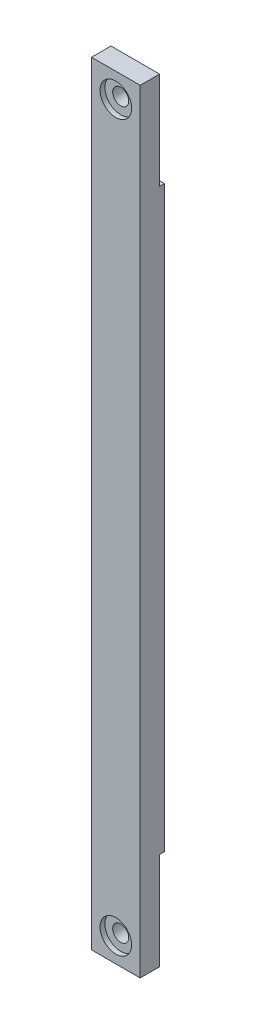
SolidWorks part; units mm, degrees
ref_plane "前视基准面" through (0, 0, 0) normal (0, 0, 1) x (1, 0, 0)
ref_plane "上视基准面" through (0, 0, 0) normal (0, 1, 0) x (1, 0, 0)
ref_plane "右视基准面" through (0, 0, 0) normal (1, 0, 0) x (0, 0, -1)
other "Configuration Table"
sketch "草图1" plane through (0, 0, 0) normal (0, 0, 1) x (1, 0, 0)
  line L1 (0, 0) -> (10, 0)
  line L2 (0, 0) -> (0, -159)
  line L3 (0, -159) -> (10, -159)
  line L4 (10, 0) -> (10, -159)
  line L5 (0, 0) -> (10, -159) construction
  line L6 (0, -159) -> (10, 0) construction
  point P4 (5, -79.5)
  dimension "D1" = 10
  dimension "D2" = 159
extrude "凸台-拉伸1" add sketch "草图1" along normal blind 5
sketch "草图3" plane through (0, 0, 0) normal (0, 0, -1) x (-1, 0, 0)
  line L0 (0, 0) -> (0, -159) construction
  line L1 (-10, 0) -> (0, 0)
  line L2 (-10, 0) -> (-10, -20)
  line L3 (-10, -20) -> (0, -20)
  line L4 (0, 0) -> (0, -20)
  line L5 (-10, 0) -> (0, -20) construction
  line L6 (-10, -20) -> (0, 0) construction
  line L8 (-10, -159) -> (0, -159)
  line L9 (-10, -159) -> (-10, -139)
  line L10 (-10, -139) -> (0, -139)
  line L11 (0, -159) -> (0, -139)
  line L12 (-10, -159) -> (0, -139) construction
  line L13 (-10, -139) -> (0, -159) construction
  point P4 (-5, -10)
  point P12 (-5, -149)
  dimension "D1" = 20
  dimension "D2" = 20
extrude "切除-拉伸1" cut sketch "草图3" against normal blind 1
sketch "草图7" plane through (0, 0, 5) normal (0, 0, 1) x (1, 0, 0)
  line L0 (10, -159) -> (10, 0) construction
  line L1 (0, 0) -> (10, 0) construction
  line L2 (0, 0) -> (0, -10) construction
  line L3 (0, -10) -> (10, -10) construction
  line L4 (10, 0) -> (10, -10) construction
  line L5 (0, 0) -> (10, -10) construction
  line L6 (0, -10) -> (10, 0) construction
  line L8 (0, -159) -> (10, -159) construction
  line L9 (0, -159) -> (0, -149) construction
  line L10 (0, -149) -> (10, -149) construction
  line L11 (10, -159) -> (10, -149) construction
  line L12 (0, -159) -> (10, -149) construction
  line L13 (0, -149) -> (10, -159) construction
  circle A0 centre (5, -5) radius 3.25
  circle A1 centre (5, -154) radius 3.25
  point P4 (5, -5)
  point P12 (5, -154)
  dimension "D3" = 6.5
  dimension "D4" = 6.5
  dimension "D1" = 10
  dimension "D2" = 10
hole_wizard "M4 螺纹孔的螺纹孔钻头1" positions "草图8" profile "草图9" hole size "M4" standard "ISO" end condition through all
sketch "草图8" plane through (0, 0, 5) normal (0, 0, 1) x (1, 0, 0)
  point P0 (5, -5)
  point P3 (5, -154)
sketch "草图9" plane through (5, -5, 5) normal (1, 0, 0) x (0, -1, 0)
  line L0 (0, 0) -> (0, 5)
  line L1 (0, 5) -> (1.65, 5)
  line L2 (1.65, 5) -> (1.65, 0)
  line L5 (1.65, 0) -> (0, 0)
  line L11 (0, -6.35) -> (0, 107.95) construction
  dimension "通孔孔直径" = 3.3
  dimension "通孔孔深度" = 5
extrude "切除-拉伸2" cut sketch "草图7" against normal blind 1
